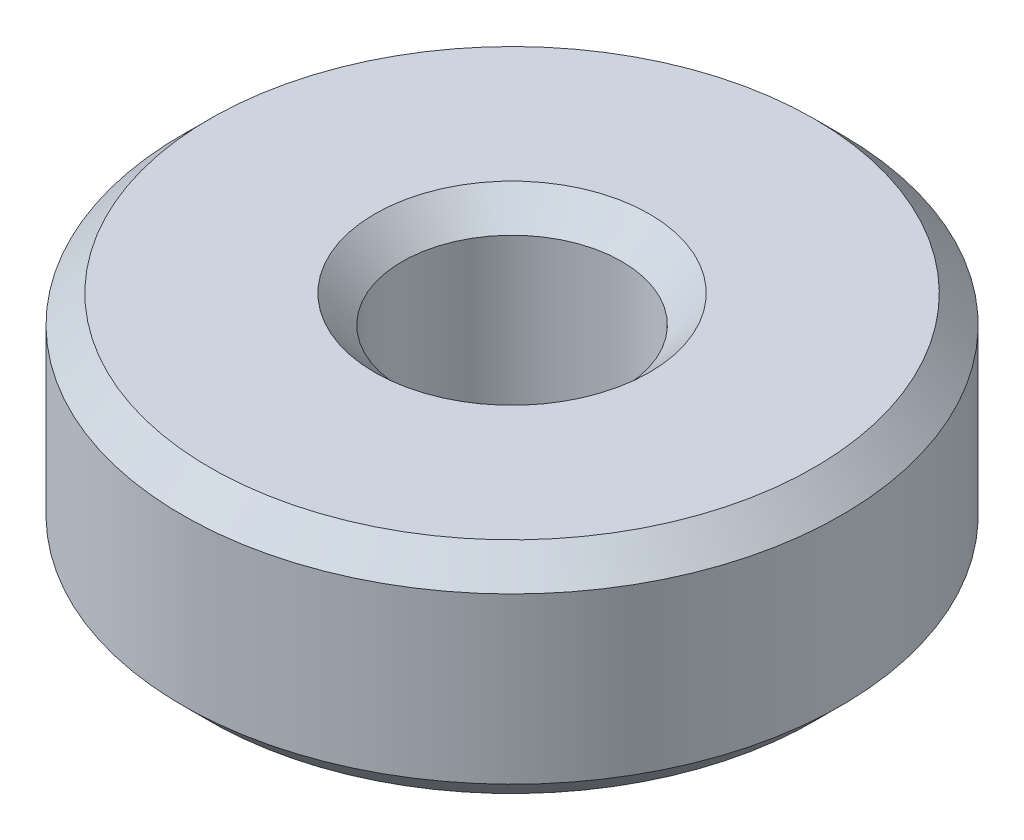
SolidWorks part; units mm, degrees
material "AISI 304"
ref_plane "Front Plane" through (0, 0, 0) normal (0, 0, 1) x (1, 0, 0)
ref_plane "Top Plane" through (0, 0, 0) normal (0, 1, 0) x (1, 0, 0)
ref_plane "Right Plane" through (0, 0, 0) normal (1, 0, 0) x (0, 0, -1)
sketch "Sketch2" plane through (0, 0, 0) normal (0, 0, 1) x (1, 0, 0)
  line L0 (0, 0) -> (0, 4) construction
  line L1 (2.5, 0) -> (5.5, 0)
  line L2 (5.5, 0) -> (6, 0.5)
  line L3 (6, 0.5) -> (6, 3.5)
  line L4 (6, 3.5) -> (5.5, 4)
  line L5 (5.5, 4) -> (2.5, 4)
  line L6 (2.5, 4) -> (2, 3.5)
  line L7 (2, 3.5) -> (2, 0.5)
  line L8 (2, 0.5) -> (2.5, 0)
  dimension "D1" = 12
  dimension "D2" = 4
  dimension "D3" = 4
  dimension "D4" = 0.5
revolve "Revolve1" add sketch "Sketch2" angle 360 about L0
